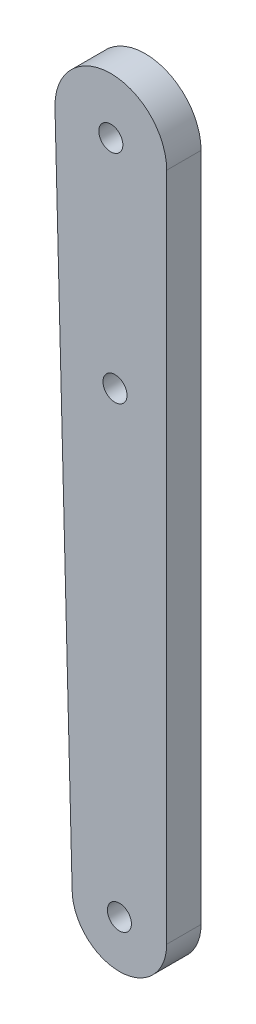
SolidWorks part; units mm, degrees
ref_plane "Front Plane" through (0, 0, 0) normal (0, 0, 1) x (1, 0, 0)
ref_plane "Top Plane" through (0, 0, 0) normal (0, 1, 0) x (1, 0, 0)
ref_plane "Right Plane" through (0, 0, 0) normal (1, 0, 0) x (0, 0, -1)
sketch "Sketch1" plane through (0, 0, 0) normal (0, 0, 1) x (1, 0, 0)
  line L6 (-0.0007, -12.9839) -> (-0.0007, 65.0161)
  line L7 (-13.0007, 65.0161) -> (-11.0007, -12.9839)
  arc A0 (-0.0007, 65.0161) -> (-13.0007, 65.0161) centre (-6.5007, 65.0161) ccw
  arc A1 (-11.0007, -12.9839) -> (-0.0007, -12.9839) centre (-5.5007, -12.9839) ccw
  circle A2 centre (-6.5007, 65.0161) radius 1.4
  circle A3 centre (-5.5007, -12.9839) radius 1.4
  circle A4 centre (-6.0128, 40.0161) radius 1.4
  point P8 (-5.5007, -18.4839)
  point P12 (-6.5007, 71.5161)
  dimension "D1" = 13
  dimension "D4" = 11
  dimension "D5" = 25
  dimension "D2" = 2.8
  dimension "D3" = 2.8
  dimension "D6" = 2.8
  dimension "D7" = 90
extrude "Boss-Extrude2" add sketch "Sketch1" along normal blind 4
